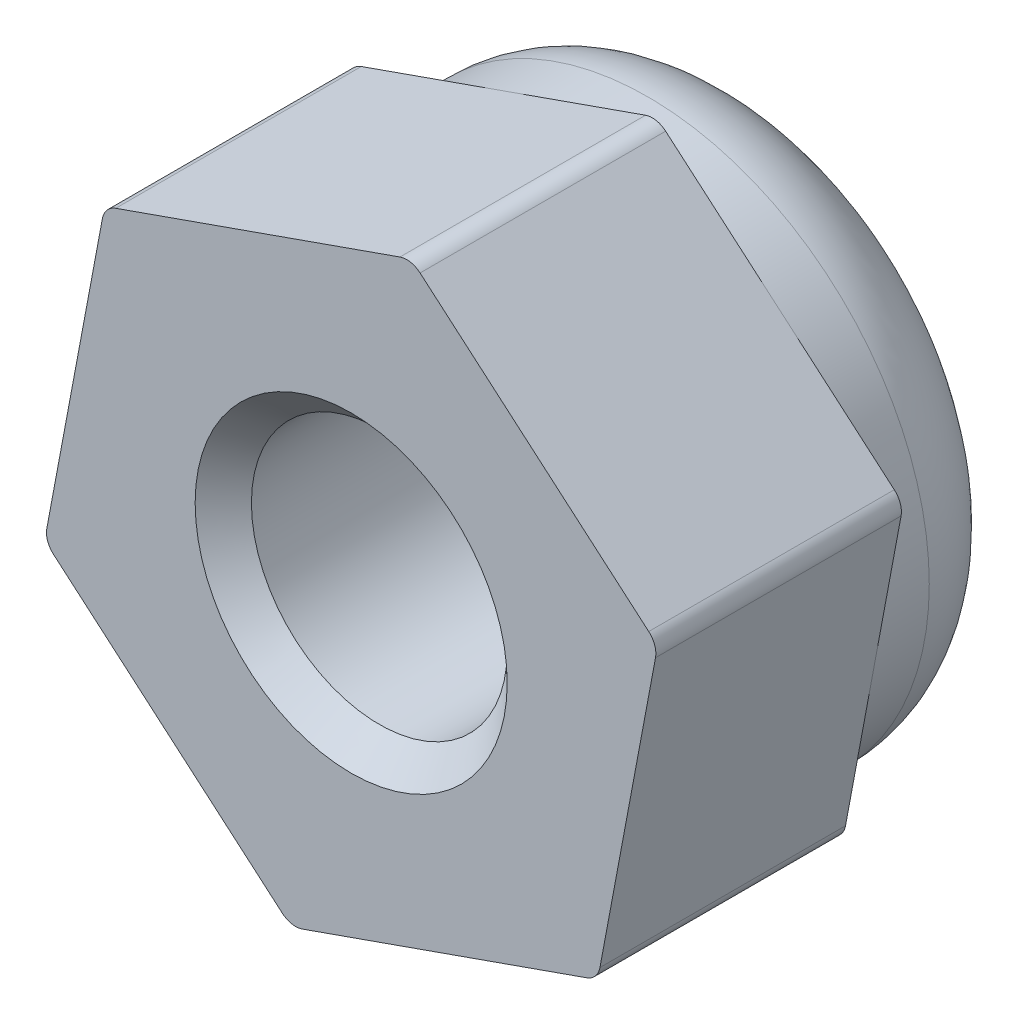
SolidWorks part; units mm, degrees
ref_plane "前视基准面" through (0, 0, 0) normal (0, 0, 1) x (1, 0, 0)
ref_plane "上视基准面" through (0, 0, 0) normal (0, 1, 0) x (1, 0, 0)
ref_plane "右视基准面" through (0, 0, 0) normal (1, 0, 0) x (0, 0, -1)
sketch "草图1" plane through (0, 0, 0) normal (0, 0, 1) x (1, 0, 0)
  line L1 (2.4099, -2.0678) -> (2.9957, 1.0532)
  line L2 (2.9957, 1.0532) -> (0.5858, 3.1209)
  line L3 (0.5858, 3.1209) -> (-2.4099, 2.0678)
  line L4 (-2.4099, 2.0678) -> (-2.9957, -1.0532)
  line L5 (-2.9957, -1.0532) -> (-0.5858, -3.1209)
  line L6 (-0.5858, -3.1209) -> (2.4099, -2.0678)
  circle A0 centre (0, 0) radius 2.75 construction
  dimension "D1" = 5.5
extrude "凸台-拉伸1" add sketch "草图1" along normal blind 2.4
sketch "草图2" plane through (0, 0, 2.4) normal (0, 0, 1) x (1, 0, 0)
  line L0 (2.9957, 1.0532) -> (0.5858, 3.1209) construction
  circle A0 centre (0, 0) radius 2.75
extrude "凸台-拉伸3" add sketch "草图2" against normal blind 3.9
fillet "圆角1" radius 1 1 edges at (2.75, 0, -1.5)
fillet "圆角2" radius 0.2 6 edges at (2.4099, -2.0678, 1.2) (2.9957, 1.0532, 1.2) (0.5858, 3.1209, 1.2) (-2.4099, 2.0678, 1.2) (-2.9957, -1.0532, 1.2) (-0.5858, -3.1209, 1.2)
hole_wizard "M3 螺纹孔1" positions "草图8" profile "草图7" tap size "M3" standard "GB"
sketch "草图8" plane through (0, 0, 2.4) normal (0, 0, 1) x (1, 0, 0)
  point P0 (0, 0)
sketch "草图7" plane through (0, 0, 2.4) normal (1, 0, 0) x (0, -1, 0)
  line L0 (0, 0) -> (0, 8.2511)
  line L1 (0, 8.2511) -> (1.25, 7.5)
  line L2 (1.25, 7.5) -> (1.25, 0.275)
  line L3 (1.25, 0.275) -> (1.525, 0)
  line L5 (1.525, 0) -> (0, 0)
  line L6 (-1.25, 0.275) -> (-1.525, 0) construction
  line L10 (0, 8.2511) -> (-1.25, 7.5) construction
  line L11 (0, -6.35) -> (0, 107.95) construction
  dimension "螺纹孔钻头直径" = 2.5
  dimension "螺纹孔钻头深度" = 7.5
  dimension "近端锥形沉头孔直径" = 3.05
  dimension "近端锥形沉头孔角度" = 90
  dimension "导头角度" = 118
cosmetic thread "孔螺蚊线2" parameters "D1"=5, "D2"=3
